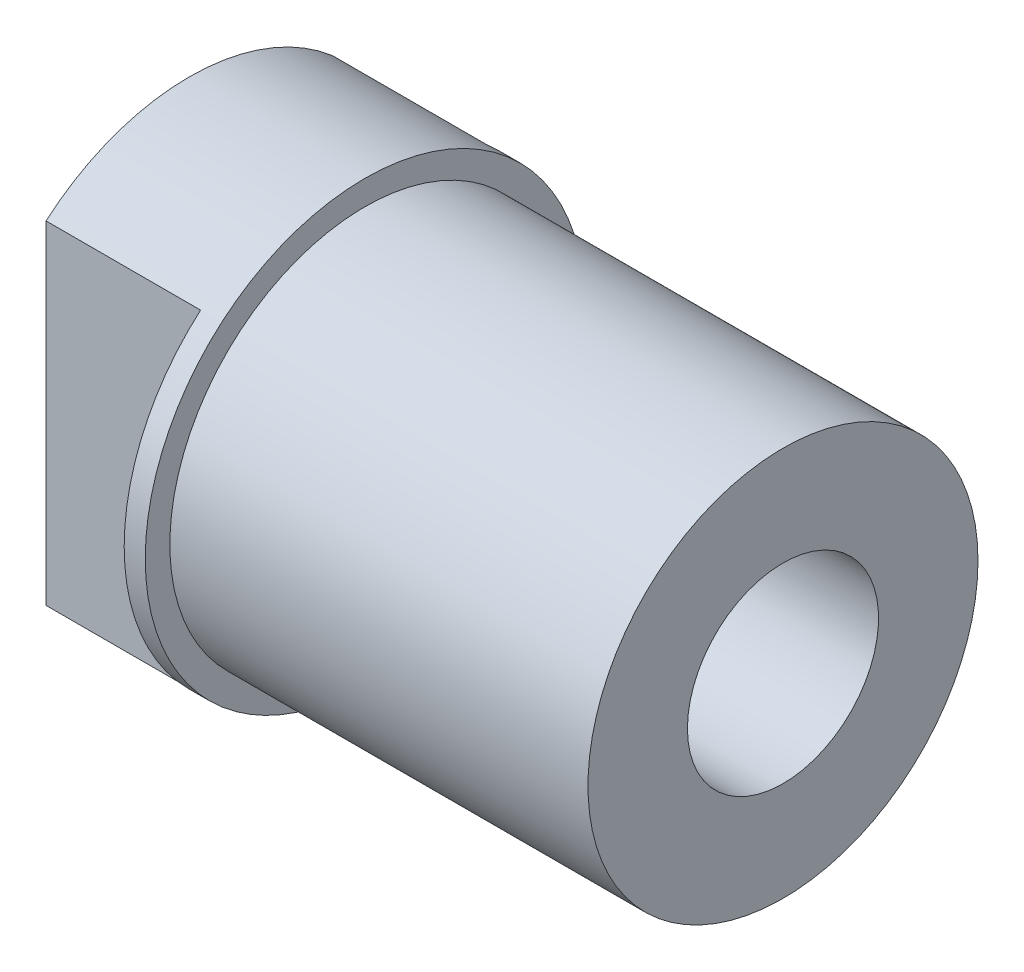
SolidWorks part; units mm, degrees
other "Markup1"
sketch "Sketch7" plane through (15.113, 7.9375, -7.9375) normal (0.8229, 0.5627, -0.0792) x (0.0116, -0.1561, -0.9877)
material "AISI 4130 Steel, normalized at 870C"
ref_plane "Top" through (0, 0, 0) normal (0, 0, 1) x (1, 0, 0)
ref_plane "Right" through (0, 0, 0) normal (0, 1, 0) x (1, 0, 0)
ref_plane "Front" through (0, 0, 0) normal (1, 0, 0) x (0, 0, -1)
sketch "Sketch2" plane through (0, 0, 0) normal (1, 0, 0) x (0, 0, -1)
  circle A0 centre (0, 0) radius 7.9375
  dimension "D1" = 15.875
extrude "Boss-Extrude1" add sketch "Sketch2" against normal blind 6.35
sketch "Sketch3" plane through (0, 0, 0) normal (1, 0, 0) x (0, 0, -1)
  circle A0 centre (0, 0) radius 7.0485
  circle A2 centre (0, 0) radius 7.9375 construction
  dimension "D1" = 0.889
extrude "Boss-Extrude2" add sketch "Sketch3" along normal blind 15.113
sketch "Sketch4" plane through (0, 0, 0) normal (0, 1, 0) x (1, 0, 0)
  line L1 (-6.35, 7.9375) -> (-0.762, 7.9375)
  line L2 (-6.35, 7.9375) -> (-6.35, 5.1752)
  line L3 (-6.35, 5.1752) -> (-0.762, 5.1752)
  line L4 (-0.762, 7.9375) -> (-0.762, 5.1752)
  line L5 (-6.35, -7.9375) -> (-0.762, -7.9375)
  line L6 (-6.35, -7.9375) -> (-6.35, -5.1752)
  line L7 (-6.35, -5.1752) -> (-0.762, -5.1752)
  line L8 (-0.762, -7.9375) -> (-0.762, -5.1752)
  dimension "D1" = 10.3505
  dimension "D2" = 5.588
extrude "Cut-Extrude1" cut sketch "Sketch4" against normal mid plane 12.7
hole_wizard "1/4-28 Tapped Hole1" [suppressed] positions "3DSketch1" profile "Sketch5" tap size "1/4-28" standard "ANSI Inch"
sketch3d "3DSketch1"
  arc A0 (-6.35, -3.6796, 5.1752) -> (-6.35, -3.6796, -5.1752) centre (-6.35, 0, 0) ccw construction
  arc A1 (-6.35, -3.6796, 5.1752) -> (-6.35, -3.6796, -5.1752) centre (-6.35, 0, 0) ccw
  point P1 (-6.35, 0, 0)
  point P4 (0, 0, 0)
  point P5 (0, 0, 0)
  point P9 (-6.35, 0, 0)
  point P12 (-6.35, 0, 0)
sketch "Sketch5" plane through (-6.35, 0, 0) normal (0, 1, 0) x (0, 0, 1)
  line L0 (0, 0) -> (0, 21.463)
  line L1 (0, 21.463) -> (2.7051, 21.463)
  line L2 (2.7051, 21.463) -> (2.7051, 0)
  line L5 (2.7051, 0) -> (0, 0)
  line L11 (0, -6.35) -> (0, 107.95) construction
  dimension "Thru Tap Drill Dia." = 5.4102
  dimension "Thru Tap Drill Depth" = 21.463
cosmetic thread "Hole Thread5" [suppressed] parameters "D2"=6.35
cosmetic thread "Hole Thread6" [suppressed] parameters "D2"=6.35
cosmetic thread "Hole Thread7" [suppressed] parameters "D2"=6.35
hole_wizard "5/16-24 Tapped Hole1" positions "3DSketch2" profile "Sketch6" tap size "5/16-24" standard "ANSI Inch" end condition through all
sketch3d "3DSketch2"
  arc A0 (-6.35, -6.0184, 5.1752) -> (-6.35, -6.0184, -5.1752) centre (-6.35, 0, 0) ccw construction
  arc A1 (-6.35, -6.0184, 5.1752) -> (-6.35, -6.0184, -5.1752) centre (-6.35, 0, 0) ccw
  point P0 (-6.35, 0, 0)
  point P6 (1.5875, 0, 0)
  point P7 (1.5875, 0, 0)
sketch "Sketch6" plane through (-6.35, 0, 0) normal (0, 1, 0) x (0, 0, 1)
  line L0 (0, 0) -> (0, 21.463)
  line L1 (0, 21.463) -> (3.4544, 21.463)
  line L2 (3.4544, 21.463) -> (3.4544, 0)
  line L5 (3.4544, 0) -> (0, 0)
  line L11 (0, -6.35) -> (0, 107.95) construction
  dimension "Thru Tap Drill Dia." = 6.9088
  dimension "Thru Tap Drill Depth" = 21.463
cosmetic thread "Hole Thread8" parameters "D2"=7.9375
equation "\"OD\"= 0.625"
equation "\"Wall\"= 0.035"
equation "\"D1@Sketch2\"=\"OD\""
equation "\"D1@Sketch3\"=\"Wall\""
